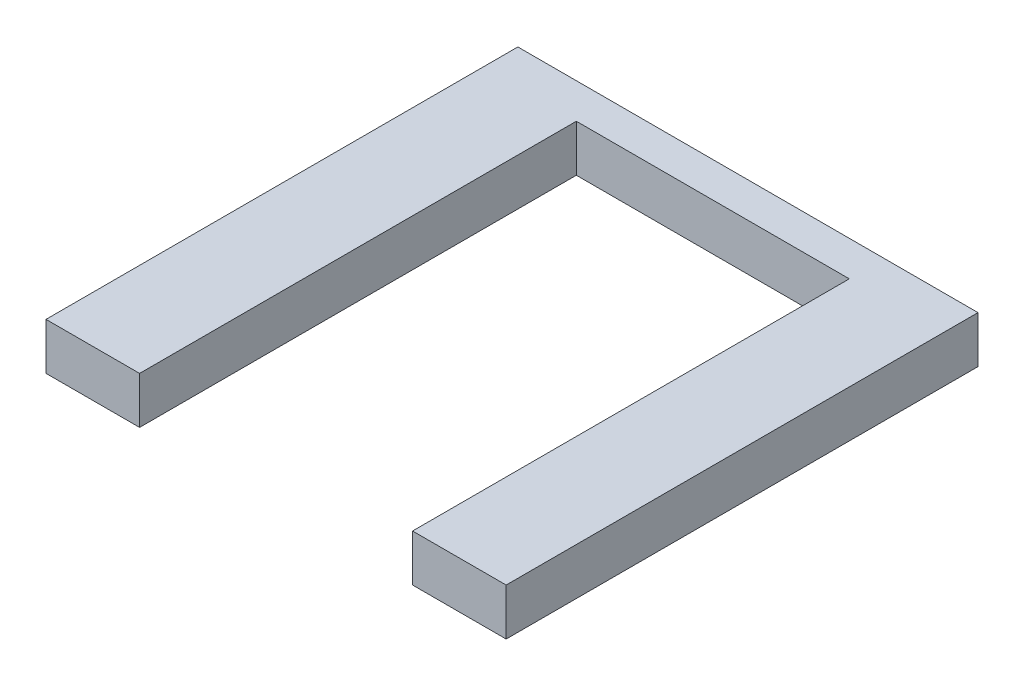
SolidWorks part; units mm, degrees
ref_plane "Front Plane" through (0, 0, 0) normal (0, 0, 1) x (1, 0, 0)
ref_plane "Top Plane" through (0, 0, 0) normal (0, 1, 0) x (1, 0, 0)
ref_plane "Right Plane" through (0, 0, 0) normal (1, 0, 0) x (0, 0, -1)
sketch "Sketch1" plane through (0, 0, 0) normal (0, 1, 0) x (1, 0, 0)
  line L1 (0, 0) -> (749.3, 0)
  line L2 (0, 0) -> (0, -768.35)
  line L3 (0, -768.35) -> (749.3, -768.35)
  line L4 (749.3, 0) -> (749.3, -768.35)
  dimension "D1" = 749.3
  dimension "D2" = 768.35
extrude "Boss-Extrude1" add sketch "Sketch1" along normal blind 76.2
sketch "Sketch2" plane through (0, 76.2, 0) normal (0, 1, 0) x (1, 0, 0)
  line L0 (0, -768.35) -> (749.3, -768.35) construction
  line L1 (152.4, -57.15) -> (596.9, -57.15)
  line L2 (152.4, -57.15) -> (152.4, -768.35)
  line L3 (152.4, -768.35) -> (596.9, -768.35)
  line L4 (596.9, -57.15) -> (596.9, -768.35)
  line L5 (0, 0) -> (0, -768.35) construction
  line L6 (749.3, -768.35) -> (749.3, 0) construction
  dimension "D1" = 711.2
  dimension "D2" = 152.4
  dimension "D3" = 152.4
extrude "Cut-Extrude1" cut sketch "Sketch2" against normal blind 76.2
